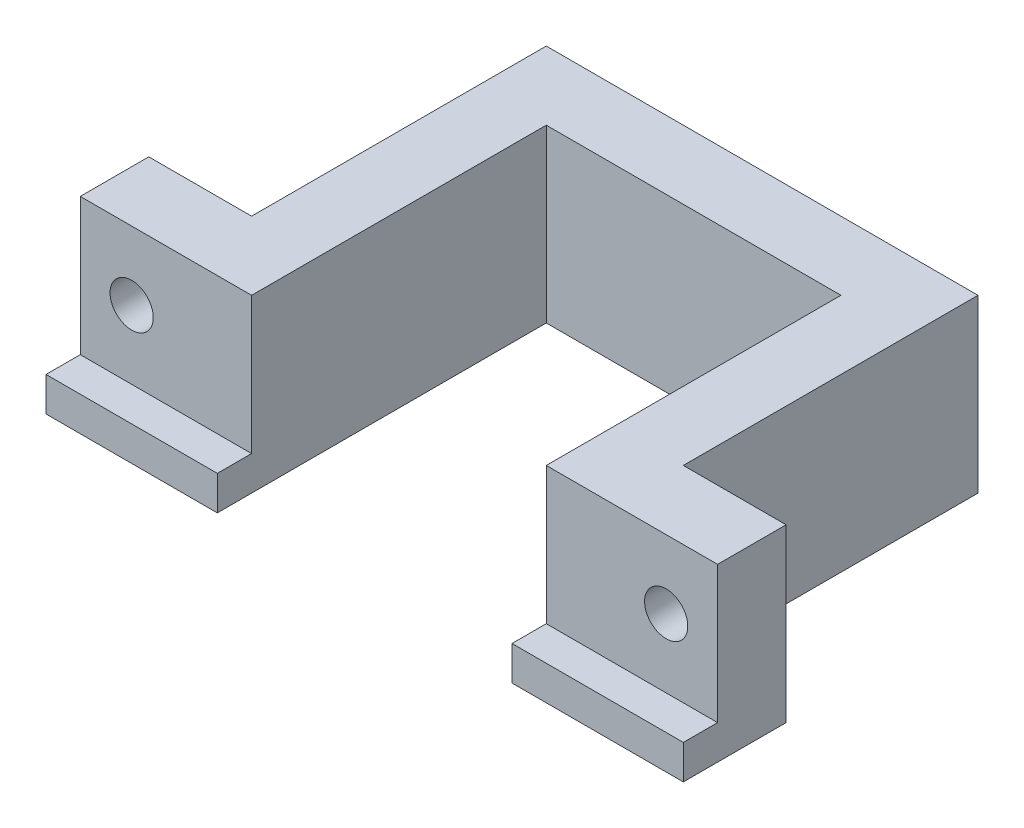
SolidWorks part; units mm, degrees
ref_plane "Front Plane" through (0, 0, 0) normal (0, 0, 1) x (1, 0, 0)
ref_plane "Top Plane" through (0, 0, 0) normal (0, 1, 0) x (1, 0, 0)
ref_plane "Right Plane" through (0, 0, 0) normal (1, 0, 0) x (0, 0, -1)
sketch "Sketch1" plane through (0, 0, 0) normal (0, 1, 0) x (1, 0, 0)
  line L0 (0, 0) -> (0, 43)
  line L1 (0, 43) -> (43, 43)
  line L2 (43, 43) -> (43, 0)
  line L3 (43, 0) -> (68, 0)
  line L4 (68, 0) -> (68, 10)
  line L5 (68, 10) -> (53, 10)
  line L6 (53, 10) -> (53, 53)
  line L7 (53, 53) -> (-10, 53)
  line L8 (-10, 53) -> (-10, 10)
  line L9 (-10, 10) -> (-25, 10)
  line L10 (-25, 10) -> (-25, 0)
  line L11 (-25, 0) -> (0, 0)
  dimension "D1" = 25
  dimension "D2" = 10
  dimension "D3" = 10
  dimension "D4" = 43
  dimension "D5" = 10
  dimension "D6" = 43
extrude "Boss-Extrude1" add sketch "Sketch1" along normal blind 20
sketch "Sketch2" plane through (0, 0, -10) normal (0, 0, -1) x (-1, 0, 0)
  line L0 (-68, 10) -> (25, 10) construction
  line L1 (-68, 20) -> (-68, 0) construction
  line L2 (25, 20) -> (25, 0) construction
  circle A0 centre (-60.5, 10) radius 3.15
  circle A1 centre (17.5, 10) radius 3.15
  dimension "D1" = 6.3
  dimension "D2" = 7.5
  dimension "D3" = 7.5
extrude "Cut-Extrude2" cut sketch "Sketch2" against normal through all
sketch "Sketch3" plane through (0, 0, -10) normal (0, 0, -1) x (-1, 0, 0)
  circle A0 centre (17.5, 10) radius 4.25
  circle A1 centre (-60.5, 10) radius 4.25
  dimension "D1" = 8.5
extrude "Cut-Extrude3" cut sketch "Sketch3" against normal blind 4
sketch "Sketch4" plane through (0, 0, 0) normal (0, -1, 0) x (1, 0, 0)
  line L0 (-25, 5) -> (0, 5)
  line L1 (43, 5) -> (68, 5)
  line L2 (-25, 0) -> (0, 0) construction
  line L3 (43, 0) -> (68, 0) construction
  line L12 (0, 0) -> (-25, 0)
  line L13 (-25, 0) -> (-25, -10)
  line L14 (-25, -10) -> (-10, -10)
  line L15 (-10, -10) -> (-10, -53)
  line L16 (-10, -53) -> (53, -53)
  line L17 (53, -53) -> (53, -10)
  line L18 (53, -10) -> (68, -10)
  line L19 (68, -10) -> (68, 0)
  line L20 (68, 0) -> (43, 0)
  line L21 (43, 0) -> (43, -43)
  line L22 (43, -43) -> (0, -43)
  line L23 (0, -43) -> (0, 0)
  line L25 (-25, 5) -> (-25, -10)
  line L26 (-25, -10) -> (-10, -10)
  line L27 (-10, -10) -> (-10, -53)
  line L28 (-10, -53) -> (53, -53)
  line L29 (53, -53) -> (53, -10)
  line L30 (53, -10) -> (68, -10)
  line L31 (68, -10) -> (68, 5)
  line L33 (43, 5) -> (43, -43)
  line L34 (43, -43) -> (0, -43)
  line L35 (0, -43) -> (0, 5)
  dimension "D2" = 5
  dimension "D3" = 5
  dimension "D1" = 0
extrude "Boss-Extrude2" add sketch "Sketch4" along normal blind 5
